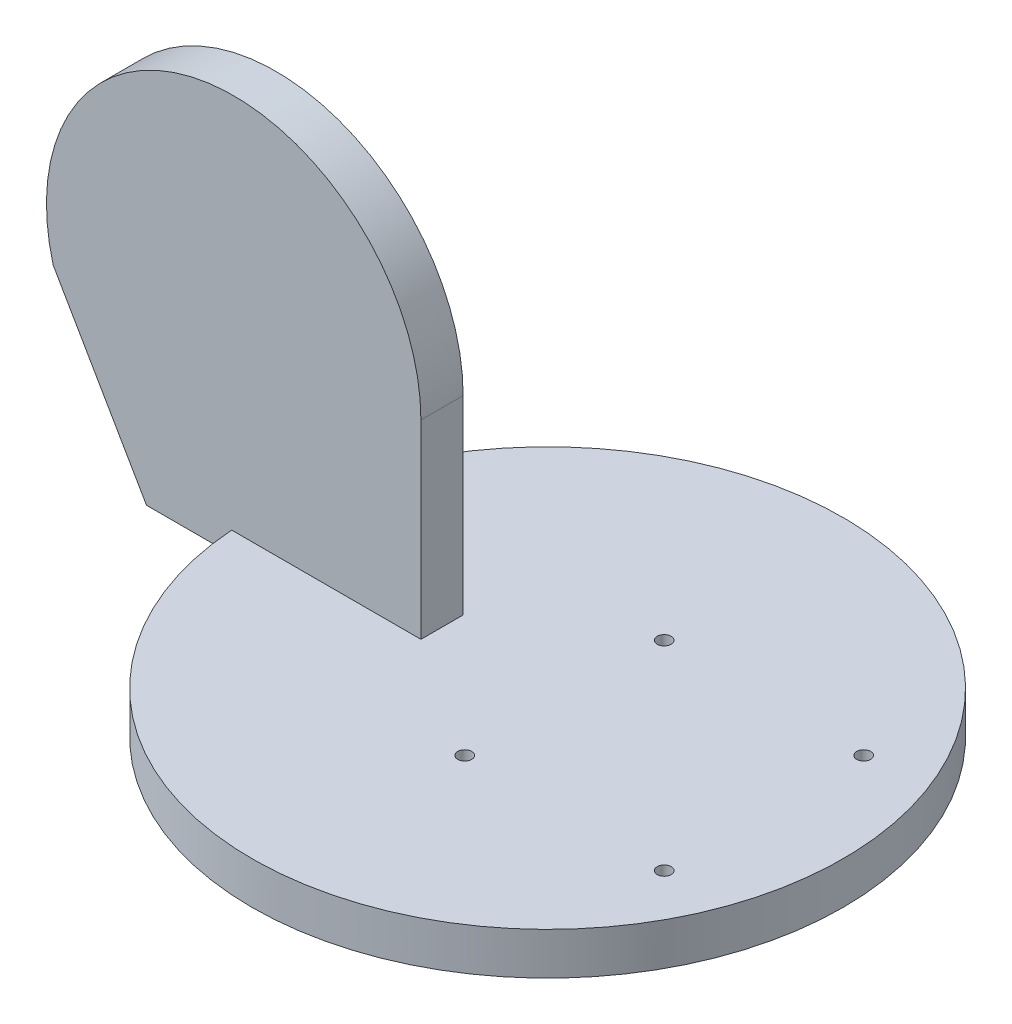
SolidWorks part; units mm, degrees
ref_plane "Front Plane" through (0, 0, 0) normal (0, 0, 1) x (1, 0, 0)
ref_plane "Top Plane" through (0, 0, 0) normal (0, 1, 0) x (1, 0, 0)
ref_plane "Right Plane" through (0, 0, 0) normal (1, 0, 0) x (0, 0, -1)
sketch "Sketch1" plane through (0, 0, 0) normal (0, 1, 0) x (1, 0, 0)
  circle A0 centre (0, 0) radius 70
  dimension "D1" = 140
extrude "Boss-Extrude1" add sketch "Sketch1" along normal blind 10
sketch "Sketch2" plane through (0, 0, 0) normal (0, -1, 0) x (1, 0, 0)
  circle A2 centre (0, 0) radius 65
  circle A3 centre (0, 0) radius 65
  dimension "D1" = 5
extrude "Boss-Extrude2" add sketch "Sketch2" along normal blind 3
sketch "Sketch3" plane through (0, 0, 0) normal (0, 0, 1) x (1, 0, 0)
  line L3 (-25, 55) -> (-25, 5)
  line L4 (-25, 5) -> (-90, 5)
  line L5 (-90, 5) -> (-112.0943, 43.2048)
  arc A2 (-112.0943, 43.2048) -> (-25, 55) centre (-69.3458, 55) cw
  dimension "D1" = 25
  dimension "D3" = 65
  dimension "D2" = 5
  dimension "D4" = 50
extrude "Boss-Extrude3" add sketch "Sketch3" along normal mid plane 10
hole_wizard "M4x0.7 Tapped Hole1" positions "Sketch4" profile "Sketch5" tap size "M4x0.7" standard "ANSI Metric"
sketch "Sketch4" plane through (0, 10, 0) normal (0, 1, 0) x (1, 0, 0)
  point P0 (4, 23.622)
  point P2 (51.244, 23.622)
  point P4 (51.244, -23.622)
  point P6 (4, -23.622)
  dimension "D1" = 47.244
  dimension "D2" = 47.244
  dimension "D3" = 4
  dimension "D4" = 23.622
sketch "Sketch5" plane through (4, 10, -23.622) normal (1, 0, 0) x (0, 0, 1)
  line L0 (0, 0) -> (0, 11.0914)
  line L1 (0, 11.0914) -> (1.65, 10.1)
  line L2 (1.65, 10.1) -> (1.65, 0)
  line L5 (1.65, 0) -> (0, 0)
  line L10 (0, 11.0914) -> (-1.65, 10.1) construction
  line L11 (0, -6.35) -> (0, 107.95) construction
  dimension "Tap Drill Dia." = 3.3
  dimension "Tap Drill Depth" = 10.1
  dimension "Drill Angle" = 118
cosmetic thread "Hole Thread1" parameters "D1"=8, "D2"=4
cosmetic thread "Hole Thread2" parameters "D1"=8, "D2"=4
cosmetic thread "Hole Thread3" parameters "D1"=8, "D2"=4
cosmetic thread "Hole Thread4" parameters "D1"=8, "D2"=4
